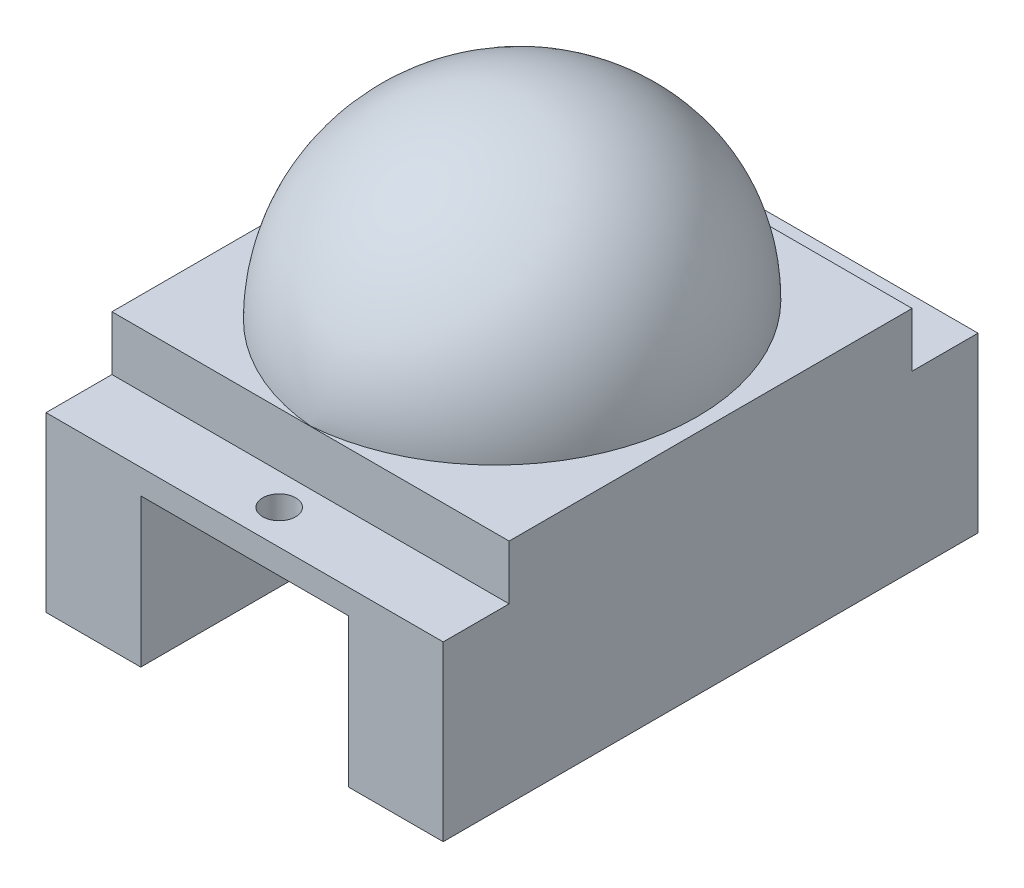
SolidWorks part; units mm, degrees
ref_plane "Front Plane" through (0, 0, 0) normal (0, 0, 1) x (1, 0, 0)
ref_plane "Top Plane" through (0, 0, 0) normal (0, 1, 0) x (1, 0, 0)
ref_plane "Right Plane" through (0, 0, 0) normal (1, 0, 0) x (0, 0, -1)
sketch "Sketch1" plane through (0, 0, 0) normal (0, 1, 0) x (1, 0, 0)
  line L1 (12.05, -16.225) -> (-12.05, -16.225)
  line L2 (12.05, -16.225) -> (12.05, 16.225)
  line L3 (12.05, 16.225) -> (-12.05, 16.225)
  line L4 (-12.05, -16.225) -> (-12.05, 16.225)
  circle A0 centre (0, 14.125) radius 1
  circle A1 centre (0, -14.125) radius 1
  point P0 (0, 0)
  dimension "D1" = 24.1
  dimension "D2" = 32.45
extrude "Boss-Extrude1" add sketch "Sketch1" along normal blind 1.5
sketch "Sketch3" plane through (0, 1.5, 0) normal (0, 1, 0) x (1, 0, 0)
  line L0 (12.05, -16.225) -> (12.05, 16.225) construction
  line L1 (-12.05, 12.225) -> (12.05, 12.225)
  line L2 (-12.05, 12.225) -> (-12.05, -12.225)
  line L3 (-12.05, -12.225) -> (12.05, -12.225)
  line L4 (12.05, 12.225) -> (12.05, -12.225)
  line L5 (-12.05, 12.225) -> (12.05, -12.225) construction
  line L6 (-12.05, -12.225) -> (12.05, 12.225) construction
  point P0 (0, 0)
  dimension "D1" = 24.45
extrude "Boss-Extrude2" add sketch "Sketch3" along normal blind 3.3
sketch "Sketch4" plane through (0, 0, 0) normal (0, -1, 0) x (1, 0, 0)
  line L0 (12.05, -16.225) -> (-12.05, -16.225) construction
  line L2 (-6.3, 16.225) -> (-6.3, -16.225)
  line L4 (6.3, 16.225) -> (6.3, -16.225)
  line L7 (12.05, 15.8155) -> (12.05, 16.225)
  line L8 (-12.05, 16.225) -> (-6.3, 16.225)
  line L9 (-12.05, 16.225) -> (-12.05, -16.225)
  line L10 (-12.05, -16.225) -> (-6.3, -16.225)
  line L11 (-6.3, 16.225) -> (-6.3, -16.225)
  line L13 (6.3, 15.8155) -> (6.3, -16.225)
  line L14 (6.3, -16.225) -> (12.05, -16.225)
  line L15 (12.05, 15.8155) -> (12.05, -16.225)
  line L16 (12.05, 16.225) -> (6.3, 16.225)
  point P0 (0, 0)
  line M2 (-12.05, 16.225) -> (-12.05, -16.225)
  line M3 (-12.05, -16.225) -> (12.05, -16.225)
  line M4 (12.05, -16.225) -> (12.05, 16.225)
  line M5 (12.05, 16.225) -> (-12.05, 16.225)
  dimension "D1" = 12.6
extrude "Boss-Extrude3" add sketch "Sketch4" along normal blind 9 contours L2 M5 M2 M3 | L4 M5 M3 M4
ref_plane "Plane1" through (0, 0, 0) normal (1, 0, 0) x (0, 0, -1)
sketch "Sketch5" plane through (0, 0, 0) normal (1, 0, 0) x (0, 0, -1)
  line L1 (-12.2084, 4.8) -> (12.225, 4.8)
  arc A1 (-12.2084, 4.8) -> (12.225, 4.8) centre (0.0083, 3.7645) cw
revolve "Revolve1" add sketch "Sketch5" angle 90 about L1 other way angle 90
